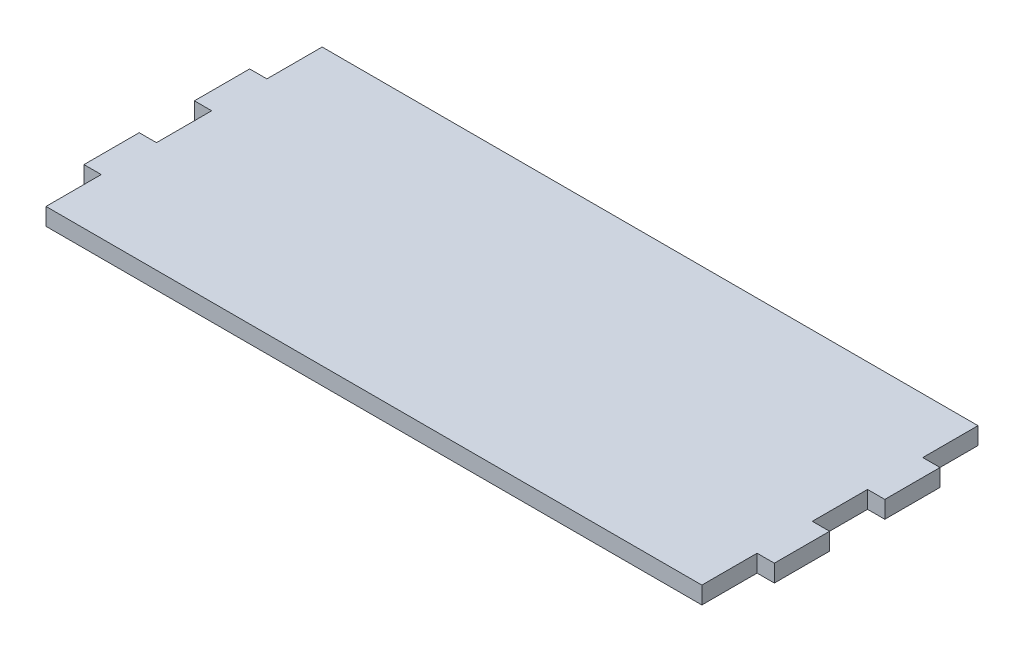
SolidWorks part; units mm, degrees
ref_plane "Front Plane" through (0, 0, 0) normal (0, 0, 1) x (1, 0, 0)
ref_plane "Top Plane" through (0, 0, 0) normal (0, 1, 0) x (1, 0, 0)
ref_plane "Right Plane" through (0, 0, 0) normal (1, 0, 0) x (0, 0, -1)
sketch "Sketch1" plane through (0, 0, 0) normal (0, 1, 0) x (1, 0, 0)
  line L0 (-122.5, 40) -> (-122.5, 24)
  line L1 (-122.5, 40) -> (67.5, 40)
  line L3 (-122.5, -40) -> (67.5, -40)
  line L4 (72.5, 24) -> (72.5, 8)
  line L5 (-72.5, 40) -> (67.5, -37.2414) construction
  line L6 (-72.5, -40) -> (72.5, 40) construction
  line L7 (67.5, 40) -> (67.5, 24)
  line L8 (-127.5, 24) -> (-127.5, 8)
  line L10 (-127.5, -8) -> (-127.5, -24)
  line L13 (67.5, 40) -> (67.5, -40) construction
  line L14 (67.5, 8) -> (67.5, -8)
  line L15 (72.5, -8) -> (72.5, -24)
  line L16 (67.5, -24) -> (67.5, -40)
  line L17 (-127.5, 24) -> (-122.5, 24)
  line L18 (-127.5, 8) -> (-122.5, 8)
  line L19 (-127.5, -8) -> (-122.5, -8)
  line L20 (-127.5, -24) -> (-122.5, -24)
  line L21 (67.5, 24) -> (72.5, 24)
  line L22 (67.5, 8) -> (72.5, 8)
  line L23 (67.5, -8) -> (72.5, -8)
  line L24 (67.5, -24) -> (72.5, -24)
  line L25 (-122.5, 8) -> (-122.5, -8)
  line L26 (-122.5, 40) -> (-122.5, -40) construction
  line L27 (-122.5, -24) -> (-122.5, -40)
  point P0 (0, 0)
  dimension "D1" = 190
  dimension "D2" = 80
  dimension "D3" = 5
  dimension "D4" = 5
extrude "Boss-Extrude1" add sketch "Sketch1" along normal blind 5
